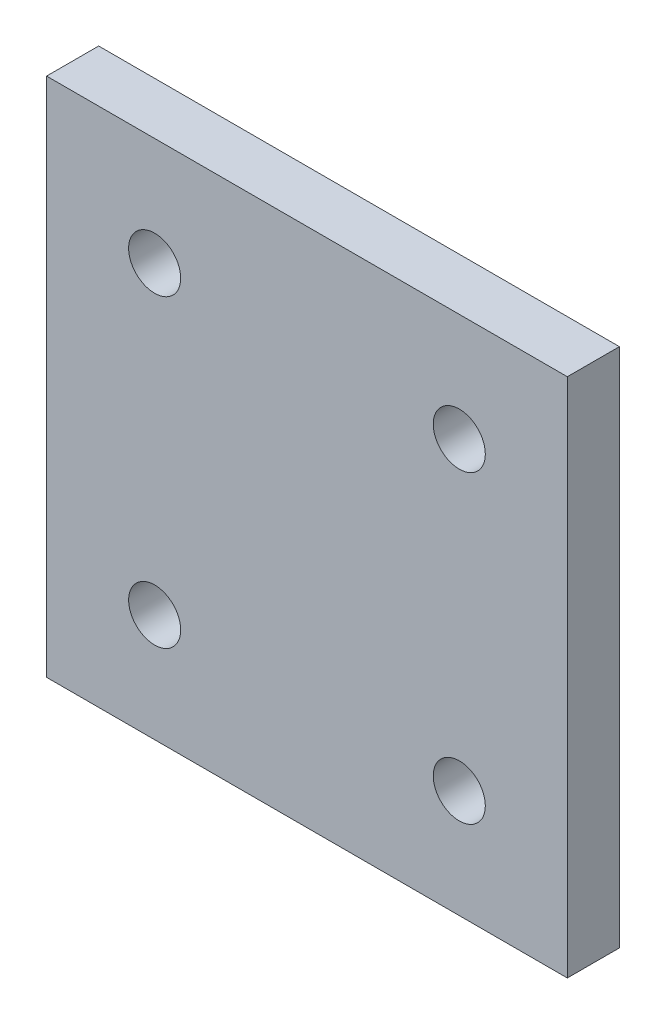
SolidWorks part; units mm, degrees
ref_plane "Płaszczyzna przednia" through (0, 0, 0) normal (0, 0, 1) x (1, 0, 0)
ref_plane "Płaszczyzna górna" through (0, 0, 0) normal (0, 1, 0) x (1, 0, 0)
ref_plane "Płaszczyzna prawa" through (0, 0, 0) normal (1, 0, 0) x (0, 0, -1)
sketch "Szkic1" plane through (0, 0, 0) normal (0, 0, 1) x (1, 0, 0)
  line L0 (55.5174, 35.3149) -> (55.5174, 20.2721)
  line L1 (-34.4826, 35.3149) -> (55.5174, 35.3149)
  line L2 (-34.4826, 35.3149) -> (-34.4826, -54.6851)
  line L3 (-34.4826, -54.6851) -> (55.5174, -54.6851)
  line L4 (55.5174, 35.3149) -> (55.5174, -54.6851)
  line L5 (-34.4826, 35.3149) -> (-24.5831, 25.4154)
  line L6 (-34.4826, -54.6851) -> (-24.5831, -44.7856)
  line L8 (55.5174, 35.3149) -> (45.6179, 25.4154)
  line L10 (55.5174, -54.6851) -> (45.6179, -44.7856)
  circle A4 centre (-24.5831, 25.4154) radius 6
  circle A5 centre (-24.5831, -44.7856) radius 6
  circle A6 centre (45.6179, -44.7856) radius 6
  circle A7 centre (45.6179, 25.4154) radius 6
  dimension "D1" = 90
  dimension "D2" = 90
extrude "Dodanie-wyciągnięcie1" add sketch "Szkic1" along normal blind 12
sketch "Szkic2" plane through (0, 0, 12) normal (0, 0, 1) x (1, 0, 0)
  line L0 (70.5174, 50.3149) -> (-49.4826, 50.3149)
  line L1 (-34.4826, 35.3149) -> (-34.4826, -54.6851)
  line L2 (70.5174, 50.3149) -> (70.5174, -69.6851)
  line L3 (70.5174, -69.6851) -> (-49.4826, -69.6851)
  line L4 (-49.4826, -69.6851) -> (-49.4826, 50.3149)
  line L5 (55.5174, 35.3149) -> (-34.4826, 35.3149)
  line L6 (-34.4826, -54.6851) -> (55.5174, -54.6851)
  line L7 (55.5174, -54.6851) -> (55.5174, 35.3149)
  point P1 (10.5174, 50.3149)
  point P13 (10.5174, 35.3149)
  dimension "D1" = 120
  dimension "D2" = 120
extrude "Dodanie-wyciągnięcie3" add sketch "Szkic2" against normal blind 12
